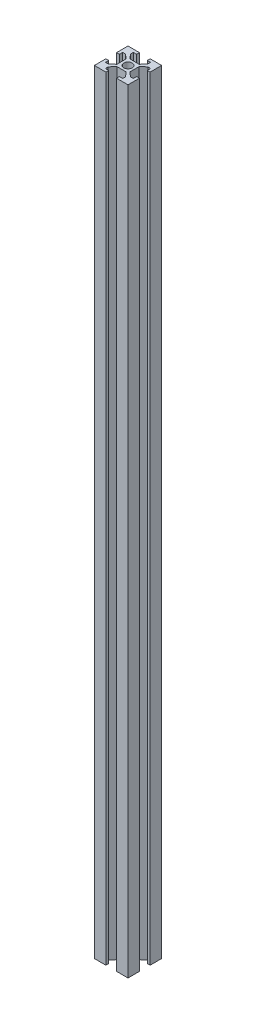
SolidWorks part; units mm, degrees
ref_plane "前视基准面" through (0, 0, 0) normal (0, 0, 1) x (1, 0, 0)
ref_plane "上视基准面" through (0, 0, 0) normal (0, 1, 0) x (1, 0, 0)
ref_plane "右视基准面" through (0, 0, 0) normal (1, 0, 0) x (0, 0, -1)
sketch "草图1" plane through (0, 0, 0) normal (0, 1, 0) x (1, 0, 0)
  line L1 (-10, 10) -> (10, 10)
  line L2 (-10, 10) -> (-10, -10)
  line L3 (-10, -10) -> (10, -10)
  line L4 (10, 10) -> (10, -10)
  line L5 (-10, 10) -> (10, -10) construction
  line L6 (-10, -10) -> (10, 10) construction
  point P0 (0, 0)
  dimension "D1" = 20
  dimension "D2" = 20
extrude "凸台-拉伸1" add sketch "草图1" along normal blind 460
sketch "草图2" plane through (0, 460, 0) normal (0, 1, 0) x (1, 0, 0)
  line L0 (0, 0) -> (0, 13.0428) construction
  line L1 (0, 0) -> (15.5008, 0) construction
  line L2 (-3.15, 10) -> (-3.15, 8.3)
  line L3 (10, 10) -> (-10, 10) construction
  line L4 (-3.15, 8.3) -> (-5.15, 8.3)
  line L5 (-5.15, 8.3) -> (-5.15, 6.6)
  line L6 (-5.15, 6.6) -> (-2.75, 3.9)
  line L7 (-2.75, 3.9) -> (2.75, 3.9)
  line L8 (-3.15, 10) -> (3.15, 10)
  line L9 (5.15, 6.6) -> (2.75, 3.9)
  line L10 (5.15, 8.3) -> (5.15, 6.6)
  line L11 (3.15, 8.3) -> (5.15, 8.3)
  line L12 (3.15, 10) -> (3.15, 8.3)
  line L13 (3.9, 2.75) -> (3.9, -2.75)
  line L14 (6.6, -5.15) -> (3.9, -2.75)
  line L15 (8.3, -5.15) -> (6.6, -5.15)
  line L16 (8.3, -3.15) -> (8.3, -5.15)
  line L17 (10, -3.15) -> (8.3, -3.15)
  line L18 (10, 3.15) -> (10, -3.15)
  line L19 (10, 3.15) -> (8.3, 3.15)
  line L20 (8.3, 3.15) -> (8.3, 5.15)
  line L21 (8.3, 5.15) -> (6.6, 5.15)
  line L22 (6.6, 5.15) -> (3.9, 2.75)
  line L23 (2.75, -3.9) -> (-2.75, -3.9)
  line L24 (-5.15, -6.6) -> (-2.75, -3.9)
  line L25 (-5.15, -8.3) -> (-5.15, -6.6)
  line L26 (-3.15, -8.3) -> (-5.15, -8.3)
  line L27 (-3.15, -10) -> (-3.15, -8.3)
  line L28 (3.15, -10) -> (-3.15, -10)
  line L29 (3.15, -10) -> (3.15, -8.3)
  line L30 (3.15, -8.3) -> (5.15, -8.3)
  line L31 (5.15, -8.3) -> (5.15, -6.6)
  line L32 (5.15, -6.6) -> (2.75, -3.9)
  line L33 (-3.9, -2.75) -> (-3.9, 2.75)
  line L34 (-6.6, 5.15) -> (-3.9, 2.75)
  line L35 (-8.3, 5.15) -> (-6.6, 5.15)
  line L36 (-8.3, 3.15) -> (-8.3, 5.15)
  line L37 (-10, 3.15) -> (-8.3, 3.15)
  line L38 (-10, -3.15) -> (-10, 3.15)
  line L39 (-10, -3.15) -> (-8.3, -3.15)
  line L40 (-8.3, -3.15) -> (-8.3, -5.15)
  line L41 (-8.3, -5.15) -> (-6.6, -5.15)
  line L42 (-6.6, -5.15) -> (-3.9, -2.75)
  circle A0 centre (0, 0) radius 2.5
  point P15 (0, 3.9)
  point P19 (0, 10)
  point P52 (0, 0)
  dimension "D1" = 5
  dimension "D2" = 3.15
  dimension "D3" = 1.7
  dimension "D4" = 2
  dimension "D5" = 1.7
  dimension "D6" = 2.75
  dimension "D7" = 6.1
  dimension "D8" = 4
extrude "切除-拉伸1" cut sketch "草图2" against normal through all
